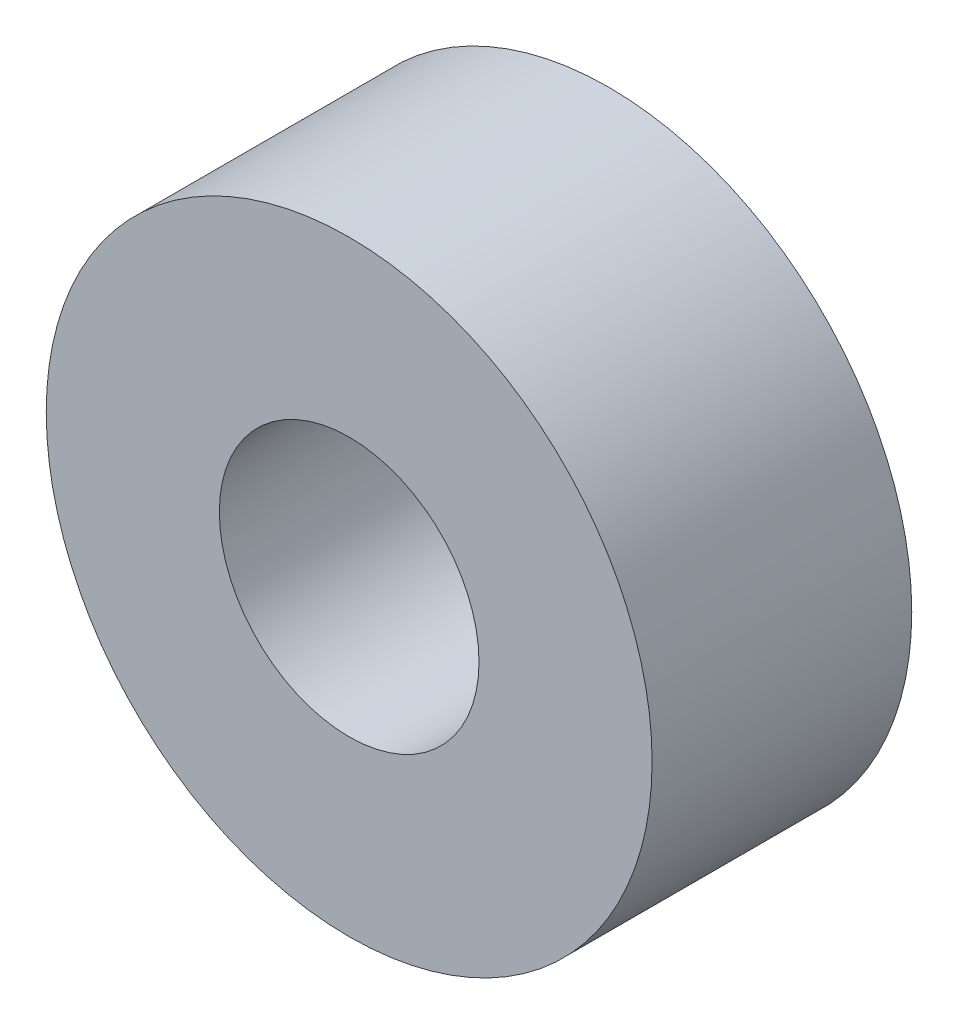
SolidWorks part; units mm, degrees
ref_plane "Front Plane" through (0, 0, 0) normal (0, 0, 1) x (1, 0, 0)
ref_plane "Top Plane" through (0, 0, 0) normal (0, 1, 0) x (1, 0, 0)
ref_plane "Right Plane" through (0, 0, 0) normal (1, 0, 0) x (0, 0, -1)
sketch "Esquisse1" plane through (0, 0, 0) normal (0, 0, 1) x (1, 0, 0)
  circle A0 centre (0, 0) radius 3.5
  circle A1 centre (0, 0) radius 1.5
  dimension "D1" = 3
  dimension "D2" = 7
extrude "Boss.-Extru.1" add sketch "Esquisse1" along normal blind 3
